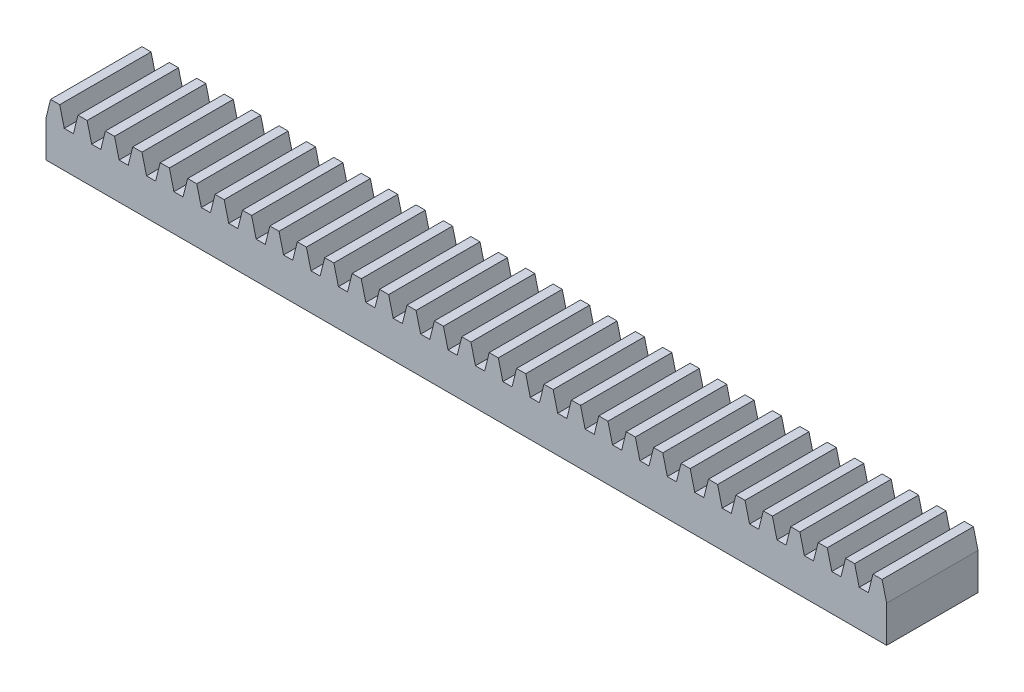
SolidWorks part; units mm, degrees
material "ABS"
ref_plane "Front Plane" through (0, 0, 0) normal (0, 0, 1) x (1, 0, 0)
ref_plane "Top Plane" through (0, 0, 0) normal (0, 1, 0) x (1, 0, 0)
ref_plane "Right Plane" through (0, 0, 0) normal (1, 0, 0) x (0, 0, -1)
sketch "Sketch1" plane through (0, 0, 0) normal (0, 0, 1) x (1, 0, 0)
  line L1 (0, 0) -> (233.68, 0)
  line L2 (0, 0) -> (0, 10.16)
  line L3 (5.08, 10.16) -> (7.62, 10.16)
  line L4 (233.68, 0) -> (233.68, 10.16)
  line L5 (5.08, 10.16) -> (3.81, 15.24)
  line L6 (3.81, 15.24) -> (1.27, 15.24)
  line L7 (1.27, 15.24) -> (0, 10.16)
  line L8 (8.89, 15.24) -> (7.62, 10.16)
  line L9 (11.43, 15.24) -> (8.89, 15.24)
  line L10 (12.7, 10.16) -> (11.43, 15.24)
  line L11 (16.51, 15.24) -> (15.24, 10.16)
  line L12 (19.05, 15.24) -> (16.51, 15.24)
  line L13 (20.32, 10.16) -> (19.05, 15.24)
  line L14 (24.13, 15.24) -> (22.86, 10.16)
  line L15 (26.67, 15.24) -> (24.13, 15.24)
  line L16 (27.94, 10.16) -> (26.67, 15.24)
  line L17 (31.75, 15.24) -> (30.48, 10.16)
  line L18 (34.29, 15.24) -> (31.75, 15.24)
  line L19 (35.56, 10.16) -> (34.29, 15.24)
  line L20 (39.37, 15.24) -> (38.1, 10.16)
  line L21 (41.91, 15.24) -> (39.37, 15.24)
  line L22 (43.18, 10.16) -> (41.91, 15.24)
  line L23 (46.99, 15.24) -> (45.72, 10.16)
  line L24 (49.53, 15.24) -> (46.99, 15.24)
  line L25 (50.8, 10.16) -> (49.53, 15.24)
  line L26 (54.61, 15.24) -> (53.34, 10.16)
  line L27 (57.15, 15.24) -> (54.61, 15.24)
  line L28 (58.42, 10.16) -> (57.15, 15.24)
  line L29 (62.23, 15.24) -> (60.96, 10.16)
  line L30 (64.77, 15.24) -> (62.23, 15.24)
  line L31 (66.04, 10.16) -> (64.77, 15.24)
  line L32 (69.85, 15.24) -> (68.58, 10.16)
  line L33 (72.39, 15.24) -> (69.85, 15.24)
  line L34 (73.66, 10.16) -> (72.39, 15.24)
  line L35 (77.47, 15.24) -> (76.2, 10.16)
  line L36 (80.01, 15.24) -> (77.47, 15.24)
  line L37 (81.28, 10.16) -> (80.01, 15.24)
  line L38 (85.09, 15.24) -> (83.82, 10.16)
  line L39 (87.63, 15.24) -> (85.09, 15.24)
  line L40 (88.9, 10.16) -> (87.63, 15.24)
  line L41 (92.71, 15.24) -> (91.44, 10.16)
  line L42 (95.25, 15.24) -> (92.71, 15.24)
  line L43 (96.52, 10.16) -> (95.25, 15.24)
  line L44 (100.33, 15.24) -> (99.06, 10.16)
  line L45 (102.87, 15.24) -> (100.33, 15.24)
  line L46 (104.14, 10.16) -> (102.87, 15.24)
  line L47 (107.95, 15.24) -> (106.68, 10.16)
  line L48 (110.49, 15.24) -> (107.95, 15.24)
  line L49 (111.76, 10.16) -> (110.49, 15.24)
  line L50 (115.57, 15.24) -> (114.3, 10.16)
  line L51 (118.11, 15.24) -> (115.57, 15.24)
  line L52 (119.38, 10.16) -> (118.11, 15.24)
  line L53 (123.19, 15.24) -> (121.92, 10.16)
  line L54 (125.73, 15.24) -> (123.19, 15.24)
  line L55 (127, 10.16) -> (125.73, 15.24)
  line L56 (130.81, 15.24) -> (129.54, 10.16)
  line L57 (133.35, 15.24) -> (130.81, 15.24)
  line L58 (134.62, 10.16) -> (133.35, 15.24)
  line L59 (138.43, 15.24) -> (137.16, 10.16)
  line L60 (140.97, 15.24) -> (138.43, 15.24)
  line L61 (142.24, 10.16) -> (140.97, 15.24)
  line L62 (146.05, 15.24) -> (144.78, 10.16)
  line L63 (148.59, 15.24) -> (146.05, 15.24)
  line L64 (149.86, 10.16) -> (148.59, 15.24)
  line L65 (153.67, 15.24) -> (152.4, 10.16)
  line L66 (156.21, 15.24) -> (153.67, 15.24)
  line L67 (157.48, 10.16) -> (156.21, 15.24)
  line L68 (161.29, 15.24) -> (160.02, 10.16)
  line L69 (163.83, 15.24) -> (161.29, 15.24)
  line L70 (165.1, 10.16) -> (163.83, 15.24)
  line L71 (168.91, 15.24) -> (167.64, 10.16)
  line L72 (171.45, 15.24) -> (168.91, 15.24)
  line L73 (172.72, 10.16) -> (171.45, 15.24)
  line L74 (176.53, 15.24) -> (175.26, 10.16)
  line L75 (179.07, 15.24) -> (176.53, 15.24)
  line L76 (180.34, 10.16) -> (179.07, 15.24)
  line L77 (184.15, 15.24) -> (182.88, 10.16)
  line L78 (186.69, 15.24) -> (184.15, 15.24)
  line L79 (187.96, 10.16) -> (186.69, 15.24)
  line L80 (191.77, 15.24) -> (190.5, 10.16)
  line L81 (194.31, 15.24) -> (191.77, 15.24)
  line L82 (195.58, 10.16) -> (194.31, 15.24)
  line L83 (199.39, 15.24) -> (198.12, 10.16)
  line L84 (201.93, 15.24) -> (199.39, 15.24)
  line L85 (203.2, 10.16) -> (201.93, 15.24)
  line L86 (207.01, 15.24) -> (205.74, 10.16)
  line L87 (209.55, 15.24) -> (207.01, 15.24)
  line L88 (210.82, 10.16) -> (209.55, 15.24)
  line L89 (214.63, 15.24) -> (213.36, 10.16)
  line L90 (217.17, 15.24) -> (214.63, 15.24)
  line L91 (218.44, 10.16) -> (217.17, 15.24)
  line L92 (222.25, 15.24) -> (220.98, 10.16)
  line L93 (224.79, 15.24) -> (222.25, 15.24)
  line L94 (226.06, 10.16) -> (224.79, 15.24)
  line L95 (229.87, 15.24) -> (228.6, 10.16)
  line L96 (232.41, 15.24) -> (229.87, 15.24)
  line L97 (233.68, 10.16) -> (232.41, 15.24)
  line L98 (149.86, 10.16) -> (152.4, 10.16)
  line L99 (157.48, 10.16) -> (160.02, 10.16)
  line L100 (165.1, 10.16) -> (167.64, 10.16)
  line L101 (241.3, 10.16) -> (240.03, 15.24) [skipped]
  line L102 (240.03, 15.24) -> (237.49, 15.24) [skipped]
  line L103 (237.49, 15.24) -> (236.22, 10.16) [skipped]
  line L104 (172.72, 10.16) -> (175.26, 10.16)
  line L105 (180.34, 10.16) -> (182.88, 10.16)
  line L106 (187.96, 10.16) -> (190.5, 10.16)
  line L107 (195.58, 10.16) -> (198.12, 10.16)
  line L108 (203.2, 10.16) -> (205.74, 10.16)
  line L109 (210.82, 10.16) -> (213.36, 10.16)
  line L110 (218.44, 10.16) -> (220.98, 10.16)
  line L111 (226.06, 10.16) -> (228.6, 10.16)
  line L112 (142.24, 10.16) -> (144.78, 10.16)
  line L113 (134.62, 10.16) -> (137.16, 10.16)
  line L114 (127, 10.16) -> (129.54, 10.16)
  line L115 (119.38, 10.16) -> (121.92, 10.16)
  line L116 (111.76, 10.16) -> (114.3, 10.16)
  line L117 (104.14, 10.16) -> (106.68, 10.16)
  line L118 (96.52, 10.16) -> (99.06, 10.16)
  line L119 (88.9, 10.16) -> (91.44, 10.16)
  line L120 (81.28, 10.16) -> (83.82, 10.16)
  line L121 (73.66, 10.16) -> (76.2, 10.16)
  line L122 (66.04, 10.16) -> (68.58, 10.16)
  line L123 (58.42, 10.16) -> (60.96, 10.16)
  line L124 (50.8, 10.16) -> (53.34, 10.16)
  line L125 (43.18, 10.16) -> (45.72, 10.16)
  line L126 (35.56, 10.16) -> (38.1, 10.16)
  line L127 (27.94, 10.16) -> (30.48, 10.16)
  line L128 (20.32, 10.16) -> (22.86, 10.16)
  line L129 (12.7, 10.16) -> (15.24, 10.16)
  point P5 (232.7606, 0)
  point P129 (0, 0)
  dimension "D1" = 10.16
  dimension "D2" = 2.54
  dimension "D3" = 5.08
  dimension "D4" = 2.54
  dimension "D5" = 5.08
  dimension "D6" = 32
extrude "Boss-Extrude1" add sketch "Sketch1" along normal blind 25.4
